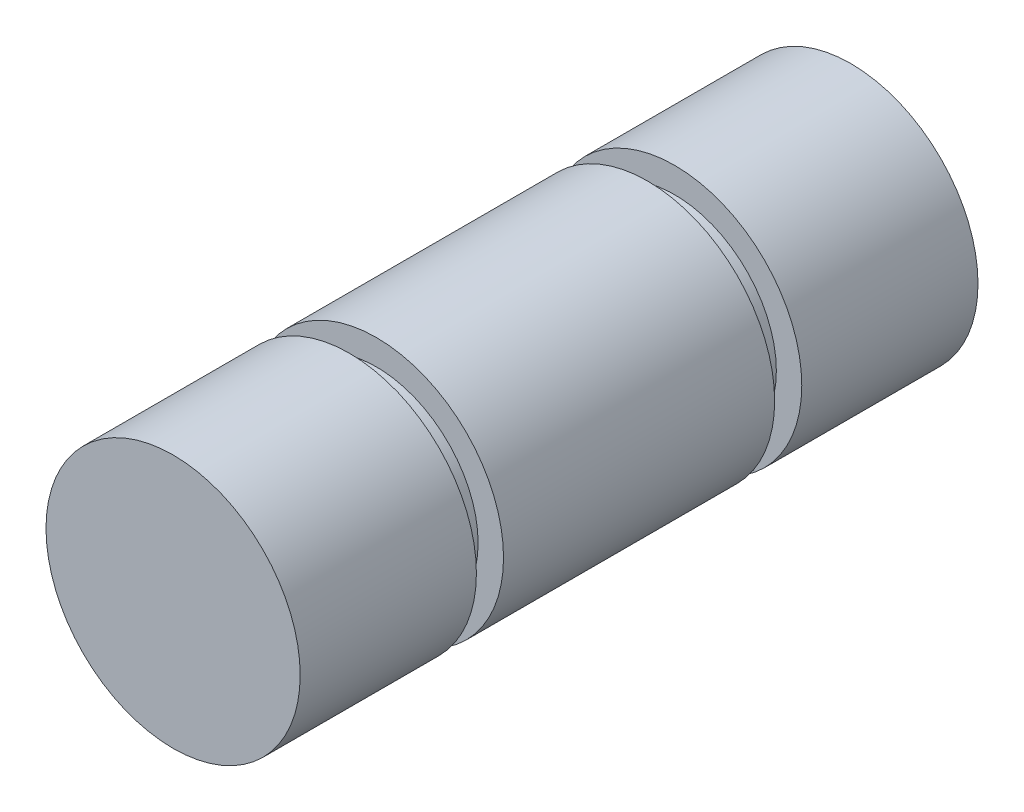
SolidWorks part; units mm, degrees
ref_plane "Front Plane" through (0, 0, 0) normal (0, 0, 1) x (1, 0, 0)
ref_plane "Top Plane" through (0, 0, 0) normal (0, 1, 0) x (1, 0, 0)
ref_plane "Right Plane" through (0, 0, 0) normal (1, 0, 0) x (0, 0, -1)
sketch "Sketch1" plane through (0, 0, 0) normal (0, 0, 1) x (1, 0, 0)
  circle A0 centre (0, 0) radius 4.7625
  dimension "D1" = 9.525
extrude "Boss-Extrude1" add sketch "Sketch1" along normal mid plane 25.4
sketch "Sketch2" plane through (0, 0, 0) normal (0, 1, 0) x (1, 0, 0)
  line L0 (4.7625, -12.7) -> (4.7625, 12.7) construction
  line L1 (4.7625, 6.096) -> (3.81, 6.096)
  line L2 (4.7625, 6.096) -> (4.7625, 5.08)
  line L3 (4.7625, 5.08) -> (3.81, 5.08)
  line L4 (3.81, 6.096) -> (3.81, 5.08)
  line L5 (4.7625, 12.7) -> (-4.7625, 12.7) construction
  line L6 (4.7625, -5.08) -> (3.81, -5.08)
  line L7 (4.7625, -5.08) -> (4.7625, -6.096)
  line L8 (4.7625, -6.096) -> (3.81, -6.096)
  line L9 (3.81, -5.08) -> (3.81, -6.096)
  line L10 (-4.7625, -12.7) -> (4.7625, -12.7) construction
  point P10 (3.81, 5.588)
  dimension "D1" = 0.9525
  dimension "D2" = 0.9525
  dimension "D3" = 1.016
  dimension "D4" = 1.016
  dimension "D5" = 6.604
  dimension "D6" = 6.604
ref_axis "Axis1" through (0, 0, 12.7) along (0, 0, -1)
revolve "Cut-Revolve1" cut sketch "Sketch2" angle 360 about axis through (0, 0, 12.7) along (0, 0, -1)
